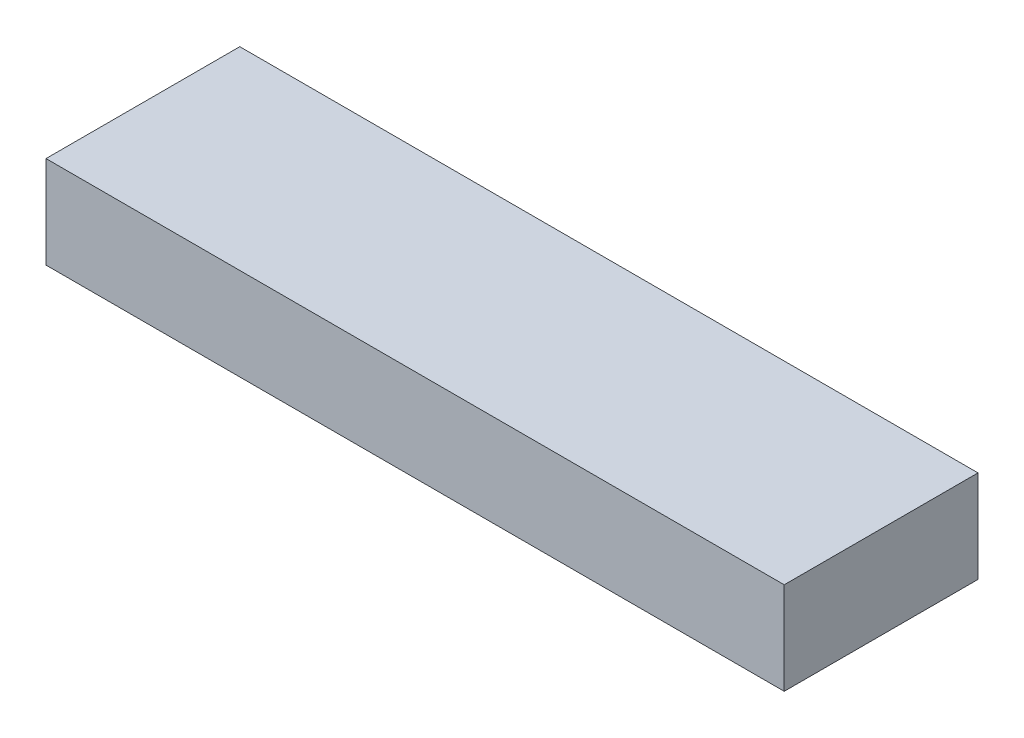
SolidWorks part; units mm, degrees
ref_plane "Спереди" through (0, 0, 0) normal (0, 0, 1) x (1, 0, 0)
ref_plane "Сверху" through (0, 0, 0) normal (0, 1, 0) x (1, 0, 0)
ref_plane "Справа" through (0, 0, 0) normal (1, 0, 0) x (0, 0, -1)
sketch "Эскиз1" plane through (0, 0, 0) normal (0, 1, 0) x (1, 0, 0)
  line L1 (-40, 10.5) -> (40, 10.5)
  line L2 (-40, 10.5) -> (-40, -10.5)
  line L3 (-40, -10.5) -> (40, -10.5)
  line L4 (40, 10.5) -> (40, -10.5)
  line L5 (-40, 10.5) -> (40, -10.5) construction
  line L6 (-40, -10.5) -> (40, 10.5) construction
  point P0 (0, 0)
extrude "Бобышка-Вытянуть1" add sketch "Эскиз1" along normal blind 10
